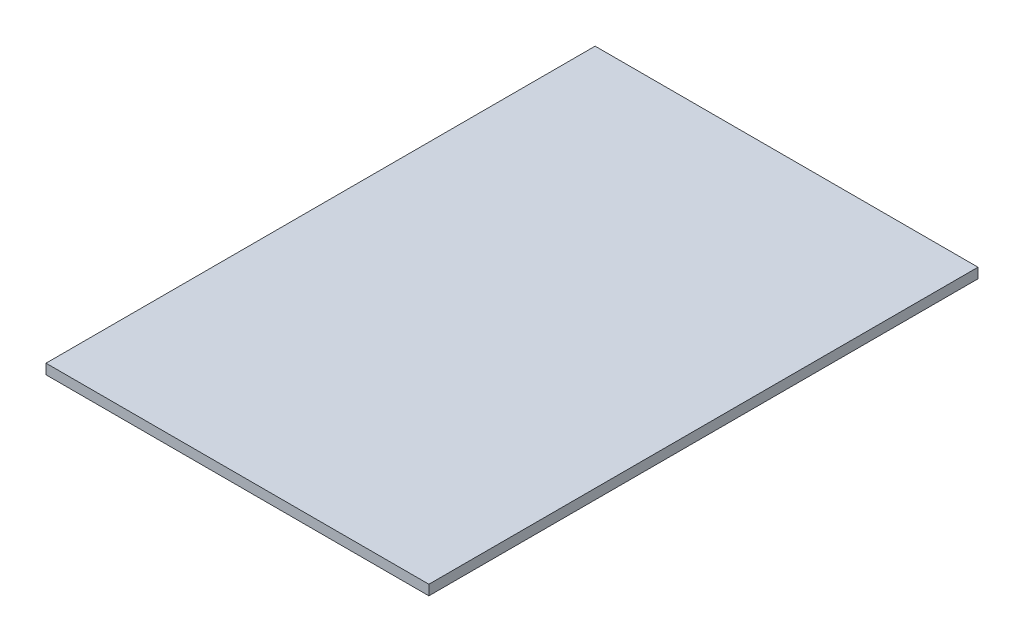
SolidWorks part; units mm, degrees
ref_plane "Front Plane" through (0, 0, 0) normal (0, 0, 1) x (1, 0, 0)
ref_plane "Top Plane" through (0, 0, 0) normal (0, 1, 0) x (1, 0, 0)
ref_plane "Right Plane" through (0, 0, 0) normal (1, 0, 0) x (0, 0, -1)
sketch "Sketch1" plane through (0, 0, 0) normal (0, 1, 0) x (1, 0, 0)
  line L0 (-74, 105) -> (-74, 109)
  line L1 (-74, 105) -> (74, 105) construction
  line L2 (-74, 105) -> (-74, -105)
  line L3 (-74, -105) -> (74, -105) construction
  line L4 (74, 105) -> (74, -105) construction
  line L5 (-74, 105) -> (74, -105) construction
  line L6 (-74, -105) -> (74, 105) construction
  line L7 (-74, 109) -> (78, 109)
  line L8 (78, 109) -> (78, -109)
  line L9 (78, -109) -> (-74, -109)
  line L10 (-74, -109) -> (-74, -105)
  line L11 (74, -105) -> (78, -105) construction
  point P0 (0, 0)
  dimension "D1" = 148
  dimension "D2" = 210
  dimension "D3" = 4
extrude "Boss-Extrude1" add sketch "Sketch1" along normal blind 4
sketch "Sketch2" plane through (0, 4, 0) normal (0, 1, 0) x (1, 0, 0)
  line L1 (72.0066, 102.0794) -> (78, 105.5397)
  line L2 (78, 105.5397) -> (78, 112.4603)
  line L3 (78, 112.4603) -> (72.0066, 115.9206)
  line L4 (72.0066, 115.9206) -> (66.0131, 112.4603)
  line L5 (66.0131, 112.4603) -> (66.0131, 105.5397)
  line L6 (66.0131, 105.5397) -> (72.0066, 102.0794)
  line L12 (72.0066, 109) -> (75.0033, 114.1905) construction
  line L19 (72.0066, 109) -> (78, 109) construction
  line L20 (78, 109) -> (-74, 109) construction
  line L21 (78, -109) -> (78, 109) construction
  line L22 (72.0066, 102.0794) -> (72.0066, 95.1587)
  line L23 (54.0262, 105.5397) -> (60.0197, 102.0794)
  line L24 (54.0262, 112.4603) -> (54.0262, 105.5397)
  line L25 (60.0197, 115.9206) -> (54.0262, 112.4603)
  line L26 (66.0131, 112.4603) -> (60.0197, 115.9206)
  line L27 (60.0197, 102.0794) -> (66.0131, 105.5397)
  line L28 (60.0197, 102.0794) -> (60.0197, 95.1587)
  line L29 (54.0262, 84.7778) -> (60.0197, 81.3175)
  line L30 (54.0262, 91.6984) -> (54.0262, 84.7778)
  line L31 (60.0197, 95.1587) -> (54.0262, 91.6984)
  line L32 (66.0131, 91.6984) -> (60.0197, 95.1587)
  line L33 (60.0197, 81.3175) -> (66.0131, 84.7778)
  line L34 (60.0197, 81.3175) -> (60.0197, 74.3968)
  line L35 (66.0131, 84.7778) -> (72.0066, 81.3175)
  line L36 (66.0131, 91.6984) -> (66.0131, 84.7778)
  line L37 (72.0066, 95.1587) -> (66.0131, 91.6984)
  line L38 (78, 91.6984) -> (72.0066, 95.1587)
  line L39 (72.0066, 81.3175) -> (78, 84.7778)
  line L40 (72.0066, 81.3175) -> (72.0066, 74.3968)
  line L41 (42.0393, 105.5397) -> (48.0328, 102.0794)
  line L42 (42.0393, 112.4603) -> (42.0393, 105.5397)
  line L43 (48.0328, 115.9206) -> (42.0393, 112.4603)
  line L44 (54.0262, 112.4603) -> (48.0328, 115.9206)
  line L45 (48.0328, 102.0794) -> (54.0262, 105.5397)
  line L46 (48.0328, 102.0794) -> (48.0328, 95.1587)
  line L47 (30.0524, 105.5397) -> (36.0459, 102.0794)
  line L48 (30.0524, 112.4603) -> (30.0524, 105.5397)
  line L49 (36.0459, 115.9206) -> (30.0524, 112.4603)
  line L50 (42.0393, 112.4603) -> (36.0459, 115.9206)
  line L51 (36.0459, 102.0794) -> (42.0393, 105.5397)
  line L52 (36.0459, 102.0794) -> (36.0459, 95.1587)
  line L53 (18.0655, 105.5397) -> (24.059, 102.0794)
  line L54 (18.0655, 112.4603) -> (18.0655, 105.5397)
  line L55 (24.059, 115.9206) -> (18.0655, 112.4603)
  line L56 (30.0524, 112.4603) -> (24.059, 115.9206)
  line L57 (24.059, 102.0794) -> (30.0524, 105.5397)
  line L58 (24.059, 102.0794) -> (24.059, 95.1587)
  line L59 (42.0393, 84.7778) -> (48.0328, 81.3175)
  line L60 (42.0393, 91.6984) -> (42.0393, 84.7778)
  line L61 (48.0328, 95.1587) -> (42.0393, 91.6984)
  line L62 (54.0262, 91.6984) -> (48.0328, 95.1587)
  line L63 (48.0328, 81.3175) -> (54.0262, 84.7778)
  line L64 (48.0328, 81.3175) -> (48.0328, 74.3968)
  line L65 (30.0524, 84.7778) -> (36.0459, 81.3175)
  line L66 (30.0524, 91.6984) -> (30.0524, 84.7778)
  line L67 (36.0459, 95.1587) -> (30.0524, 91.6984)
  line L68 (42.0393, 91.6984) -> (36.0459, 95.1587)
  line L69 (36.0459, 81.3175) -> (42.0393, 84.7778)
  line L70 (36.0459, 81.3175) -> (36.0459, 74.3968)
  line L71 (18.0655, 84.7778) -> (24.059, 81.3175)
  line L72 (18.0655, 91.6984) -> (18.0655, 84.7778)
  line L73 (24.059, 95.1587) -> (18.0655, 91.6984)
  line L74 (30.0524, 91.6984) -> (24.059, 95.1587)
  line L75 (24.059, 81.3175) -> (30.0524, 84.7778)
  line L76 (24.059, 81.3175) -> (24.059, 74.3968)
  line L77 (6.0787, 105.5397) -> (12.0721, 102.0794)
  line L78 (6.0787, 112.4603) -> (6.0787, 105.5397)
  line L79 (12.0721, 115.9206) -> (6.0787, 112.4603)
  line L80 (18.0655, 112.4603) -> (12.0721, 115.9206)
  line L81 (12.0721, 102.0794) -> (18.0655, 105.5397)
  line L82 (12.0721, 102.0794) -> (12.0721, 95.1587)
  line L83 (-5.9082, 105.5397) -> (0.0852, 102.0794)
  line L84 (-5.9082, 112.4603) -> (-5.9082, 105.5397)
  line L85 (0.0852, 115.9206) -> (-5.9082, 112.4603)
  line L86 (6.0787, 112.4603) -> (0.0852, 115.9206)
  line L87 (0.0852, 102.0794) -> (6.0787, 105.5397)
  line L88 (0.0852, 102.0794) -> (0.0852, 95.1587)
  line L89 (-17.8951, 105.5397) -> (-11.9017, 102.0794)
  line L90 (-17.8951, 112.4603) -> (-17.8951, 105.5397)
  line L91 (-11.9017, 115.9206) -> (-17.8951, 112.4603)
  line L92 (-5.9082, 112.4603) -> (-11.9017, 115.9206)
  line L93 (-11.9017, 102.0794) -> (-5.9082, 105.5397)
  line L94 (-11.9017, 102.0794) -> (-11.9017, 95.1587)
  line L95 (-29.882, 105.5397) -> (-23.8886, 102.0794)
  line L96 (-29.882, 112.4603) -> (-29.882, 105.5397)
  line L97 (-23.8886, 115.9206) -> (-29.882, 112.4603)
  line L98 (-17.8951, 112.4603) -> (-23.8886, 115.9206)
  line L99 (-23.8886, 102.0794) -> (-17.8951, 105.5397)
  line L100 (-23.8886, 102.0794) -> (-23.8886, 95.1587)
  line L101 (-41.8689, 105.5397) -> (-35.8755, 102.0794)
  line L102 (-41.8689, 112.4603) -> (-41.8689, 105.5397)
  line L103 (-35.8755, 115.9206) -> (-41.8689, 112.4603)
  line L104 (-29.882, 112.4603) -> (-35.8755, 115.9206)
  line L105 (-35.8755, 102.0794) -> (-29.882, 105.5397)
  line L106 (-35.8755, 102.0794) -> (-35.8755, 95.1587)
  line L107 (-53.8558, 105.5397) -> (-47.8624, 102.0794)
  line L108 (-53.8558, 112.4603) -> (-53.8558, 105.5397)
  line L109 (-47.8624, 115.9206) -> (-53.8558, 112.4603)
  line L110 (-41.8689, 112.4603) -> (-47.8624, 115.9206)
  line L111 (-47.8624, 102.0794) -> (-41.8689, 105.5397)
  line L112 (-47.8624, 102.0794) -> (-47.8624, 95.1587)
  line L113 (60.0197, -112.4603) -> (72.0066, -105.5397)
  line L114 (-74, -109) -> (78, -109) construction
  line L119 (6.0787, 84.7778) -> (12.0721, 81.3175)
  line L120 (6.0787, 91.6984) -> (6.0787, 84.7778)
  line L121 (12.0721, 95.1587) -> (6.0787, 91.6984)
  line L122 (18.0655, 91.6984) -> (12.0721, 95.1587)
  line L123 (12.0721, 81.3175) -> (18.0655, 84.7778)
  line L124 (12.0721, 81.3175) -> (12.0721, 74.3968)
  line L125 (-5.9082, 84.7778) -> (0.0852, 81.3175)
  line L126 (-5.9082, 91.6984) -> (-5.9082, 84.7778)
  line L127 (0.0852, 95.1587) -> (-5.9082, 91.6984)
  line L128 (6.0787, 91.6984) -> (0.0852, 95.1587)
  line L129 (0.0852, 81.3175) -> (6.0787, 84.7778)
  line L130 (0.0852, 81.3175) -> (0.0852, 74.3968)
  line L131 (-17.8951, 84.7778) -> (-11.9017, 81.3175)
  line L132 (-17.8951, 91.6984) -> (-17.8951, 84.7778)
  line L133 (-11.9017, 95.1587) -> (-17.8951, 91.6984)
  line L134 (-5.9082, 91.6984) -> (-11.9017, 95.1587)
  line L135 (-11.9017, 81.3175) -> (-5.9082, 84.7778)
  line L136 (-11.9017, 81.3175) -> (-11.9017, 74.3968)
  line L137 (-29.882, 84.7778) -> (-23.8886, 81.3175)
  line L138 (-29.882, 91.6984) -> (-29.882, 84.7778)
  line L139 (-23.8886, 95.1587) -> (-29.882, 91.6984)
  line L140 (-17.8951, 91.6984) -> (-23.8886, 95.1587)
  line L141 (-23.8886, 81.3175) -> (-17.8951, 84.7778)
  line L142 (-23.8886, 81.3175) -> (-23.8886, 74.3968)
  line L143 (-41.8689, 84.7778) -> (-35.8755, 81.3175)
  line L144 (-41.8689, 91.6984) -> (-41.8689, 84.7778)
  line L145 (-35.8755, 95.1587) -> (-41.8689, 91.6984)
  line L146 (-29.882, 91.6984) -> (-35.8755, 95.1587)
  line L147 (-35.8755, 81.3175) -> (-29.882, 84.7778)
  line L148 (-35.8755, 81.3175) -> (-35.8755, 74.3968)
  line L149 (-53.8558, 84.7778) -> (-47.8624, 81.3175)
  line L150 (-53.8558, 91.6984) -> (-53.8558, 84.7778)
  line L151 (-47.8624, 95.1587) -> (-53.8558, 91.6984)
  line L152 (-41.8689, 91.6984) -> (-47.8624, 95.1587)
  line L153 (-47.8624, 81.3175) -> (-41.8689, 84.7778)
  line L154 (-47.8624, 81.3175) -> (-47.8624, 74.3968)
  line L161 (66.0131, 64.0159) -> (72.0066, 60.5556)
  line L162 (66.0131, 70.9365) -> (66.0131, 64.0159)
  line L163 (72.0066, 74.3968) -> (66.0131, 70.9365)
  line L164 (78, 70.9365) -> (72.0066, 74.3968)
  line L165 (72.0066, 60.5556) -> (78, 64.0159)
  line L166 (72.0066, 60.5556) -> (72.0066, 53.6349)
  line L167 (54.0262, 64.0159) -> (60.0197, 60.5556)
  line L168 (54.0262, 70.9365) -> (54.0262, 64.0159)
  line L169 (60.0197, 74.3968) -> (54.0262, 70.9365)
  line L170 (66.0131, 70.9365) -> (60.0197, 74.3968)
  line L171 (60.0197, 60.5556) -> (66.0131, 64.0159)
  line L172 (60.0197, 60.5556) -> (60.0197, 53.6349)
  line L173 (42.0393, 64.0159) -> (48.0328, 60.5556)
  line L174 (42.0393, 70.9365) -> (42.0393, 64.0159)
  line L175 (48.0328, 74.3968) -> (42.0393, 70.9365)
  line L176 (54.0262, 70.9365) -> (48.0328, 74.3968)
  line L177 (48.0328, 60.5556) -> (54.0262, 64.0159)
  line L178 (48.0328, 60.5556) -> (48.0328, 53.6349)
  line L179 (30.0524, 64.0159) -> (36.0459, 60.5556)
  line L180 (30.0524, 70.9365) -> (30.0524, 64.0159)
  line L181 (36.0459, 74.3968) -> (30.0524, 70.9365)
  line L182 (42.0393, 70.9365) -> (36.0459, 74.3968)
  line L183 (36.0459, 60.5556) -> (42.0393, 64.0159)
  line L184 (36.0459, 60.5556) -> (36.0459, 53.6349)
  line L185 (18.0655, 64.0159) -> (24.059, 60.5556)
  line L186 (18.0655, 70.9365) -> (18.0655, 64.0159)
  line L187 (24.059, 74.3968) -> (18.0655, 70.9365)
  line L188 (30.0524, 70.9365) -> (24.059, 74.3968)
  line L189 (24.059, 60.5556) -> (30.0524, 64.0159)
  line L190 (24.059, 60.5556) -> (24.059, 53.6349)
  line L191 (6.0787, 64.0159) -> (12.0721, 60.5556)
  line L192 (6.0787, 70.9365) -> (6.0787, 64.0159)
  line L193 (12.0721, 74.3968) -> (6.0787, 70.9365)
  line L194 (18.0655, 70.9365) -> (12.0721, 74.3968)
  line L195 (12.0721, 60.5556) -> (18.0655, 64.0159)
  line L196 (12.0721, 60.5556) -> (12.0721, 53.6349)
  line L197 (-5.9082, 64.0159) -> (0.0852, 60.5556)
  line L198 (-5.9082, 70.9365) -> (-5.9082, 64.0159)
  line L199 (0.0852, 74.3968) -> (-5.9082, 70.9365)
  line L200 (6.0787, 70.9365) -> (0.0852, 74.3968)
  line L201 (0.0852, 60.5556) -> (6.0787, 64.0159)
  line L202 (0.0852, 60.5556) -> (0.0852, 53.6349)
  line L203 (-17.8951, 64.0159) -> (-11.9017, 60.5556)
  line L204 (-17.8951, 70.9365) -> (-17.8951, 64.0159)
  line L205 (-11.9017, 74.3968) -> (-17.8951, 70.9365)
  line L206 (-5.9082, 70.9365) -> (-11.9017, 74.3968)
  line L207 (-11.9017, 60.5556) -> (-5.9082, 64.0159)
  line L208 (-11.9017, 60.5556) -> (-11.9017, 53.6349)
  line L209 (-29.882, 64.0159) -> (-23.8886, 60.5556)
  line L210 (-29.882, 70.9365) -> (-29.882, 64.0159)
  line L211 (-23.8886, 74.3968) -> (-29.882, 70.9365)
  line L212 (-17.8951, 70.9365) -> (-23.8886, 74.3968)
  line L213 (-23.8886, 60.5556) -> (-17.8951, 64.0159)
  line L214 (-23.8886, 60.5556) -> (-23.8886, 53.6349)
  line L215 (-41.8689, 64.0159) -> (-35.8755, 60.5556)
  line L216 (-41.8689, 70.9365) -> (-41.8689, 64.0159)
  line L217 (-35.8755, 74.3968) -> (-41.8689, 70.9365)
  line L218 (-29.882, 70.9365) -> (-35.8755, 74.3968)
  line L219 (-35.8755, 60.5556) -> (-29.882, 64.0159)
  line L220 (-35.8755, 60.5556) -> (-35.8755, 53.6349)
  line L221 (-53.8558, 64.0159) -> (-47.8624, 60.5556)
  line L222 (-53.8558, 70.9365) -> (-53.8558, 64.0159)
  line L223 (-47.8624, 74.3968) -> (-53.8558, 70.9365)
  line L224 (-41.8689, 70.9365) -> (-47.8624, 74.3968)
  line L225 (-47.8624, 60.5556) -> (-41.8689, 64.0159)
  line L226 (-47.8624, 60.5556) -> (-47.8624, 53.6349)
  line L233 (66.0131, 43.254) -> (72.0066, 39.7937)
  line L234 (66.0131, 50.1746) -> (66.0131, 43.254)
  line L235 (72.0066, 53.6349) -> (66.0131, 50.1746)
  line L236 (78, 50.1746) -> (72.0066, 53.6349)
  line L237 (72.0066, 39.7937) -> (78, 43.254)
  line L238 (72.0066, 39.7937) -> (72.0066, 32.873)
  line L239 (54.0262, 43.254) -> (60.0197, 39.7937)
  line L240 (54.0262, 50.1746) -> (54.0262, 43.254)
  line L241 (60.0197, 53.6349) -> (54.0262, 50.1746)
  line L242 (66.0131, 50.1746) -> (60.0197, 53.6349)
  line L243 (60.0197, 39.7937) -> (66.0131, 43.254)
  line L244 (60.0197, 39.7937) -> (60.0197, 32.873)
  line L245 (42.0393, 43.254) -> (48.0328, 39.7937)
  line L246 (42.0393, 50.1746) -> (42.0393, 43.254)
  line L247 (48.0328, 53.6349) -> (42.0393, 50.1746)
  line L248 (54.0262, 50.1746) -> (48.0328, 53.6349)
  line L249 (48.0328, 39.7937) -> (54.0262, 43.254)
  line L250 (48.0328, 39.7937) -> (48.0328, 32.873)
  line L251 (30.0524, 43.254) -> (36.0459, 39.7937)
  line L252 (30.0524, 50.1746) -> (30.0524, 43.254)
  line L253 (36.0459, 53.6349) -> (30.0524, 50.1746)
  line L254 (42.0393, 50.1746) -> (36.0459, 53.6349)
  line L255 (36.0459, 39.7937) -> (42.0393, 43.254)
  line L256 (36.0459, 39.7937) -> (36.0459, 32.873)
  line L257 (18.0655, 43.254) -> (24.059, 39.7937)
  line L258 (18.0655, 50.1746) -> (18.0655, 43.254)
  line L259 (24.059, 53.6349) -> (18.0655, 50.1746)
  line L260 (30.0524, 50.1746) -> (24.059, 53.6349)
  line L261 (24.059, 39.7937) -> (30.0524, 43.254)
  line L262 (24.059, 39.7937) -> (24.059, 32.873)
  line L263 (6.0787, 43.254) -> (12.0721, 39.7937)
  line L264 (6.0787, 50.1746) -> (6.0787, 43.254)
  line L265 (12.0721, 53.6349) -> (6.0787, 50.1746)
  line L266 (18.0655, 50.1746) -> (12.0721, 53.6349)
  line L267 (12.0721, 39.7937) -> (18.0655, 43.254)
  line L268 (12.0721, 39.7937) -> (12.0721, 32.873)
  line L269 (-5.9082, 43.254) -> (0.0852, 39.7937)
  line L270 (-5.9082, 50.1746) -> (-5.9082, 43.254)
  line L271 (0.0852, 53.6349) -> (-5.9082, 50.1746)
  line L272 (6.0787, 50.1746) -> (0.0852, 53.6349)
  line L273 (0.0852, 39.7937) -> (6.0787, 43.254)
  line L274 (0.0852, 39.7937) -> (0.0852, 32.873)
  line L275 (-17.8951, 43.254) -> (-11.9017, 39.7937)
  line L276 (-17.8951, 50.1746) -> (-17.8951, 43.254)
  line L277 (-11.9017, 53.6349) -> (-17.8951, 50.1746)
  line L278 (-5.9082, 50.1746) -> (-11.9017, 53.6349)
  line L279 (-11.9017, 39.7937) -> (-5.9082, 43.254)
  line L280 (-11.9017, 39.7937) -> (-11.9017, 32.873)
  line L281 (-29.882, 43.254) -> (-23.8886, 39.7937)
  line L282 (-29.882, 50.1746) -> (-29.882, 43.254)
  line L283 (-23.8886, 53.6349) -> (-29.882, 50.1746)
  line L284 (-17.8951, 50.1746) -> (-23.8886, 53.6349)
  line L285 (-23.8886, 39.7937) -> (-17.8951, 43.254)
  line L286 (-23.8886, 39.7937) -> (-23.8886, 32.873)
  line L287 (-41.8689, 43.254) -> (-35.8755, 39.7937)
  line L288 (-41.8689, 50.1746) -> (-41.8689, 43.254)
  line L289 (-35.8755, 53.6349) -> (-41.8689, 50.1746)
  line L290 (-29.882, 50.1746) -> (-35.8755, 53.6349)
  line L291 (-35.8755, 39.7937) -> (-29.882, 43.254)
  line L292 (-35.8755, 39.7937) -> (-35.8755, 32.873)
  line L293 (-53.8558, 43.254) -> (-47.8624, 39.7937)
  line L294 (-53.8558, 50.1746) -> (-53.8558, 43.254)
  line L295 (-47.8624, 53.6349) -> (-53.8558, 50.1746)
  line L296 (-41.8689, 50.1746) -> (-47.8624, 53.6349)
  line L297 (-47.8624, 39.7937) -> (-41.8689, 43.254)
  line L298 (-47.8624, 39.7937) -> (-47.8624, 32.873)
  line L305 (66.0131, 22.4921) -> (72.0066, 19.0317)
  line L306 (66.0131, 29.4127) -> (66.0131, 22.4921)
  line L307 (72.0066, 32.873) -> (66.0131, 29.4127)
  line L308 (78, 29.4127) -> (72.0066, 32.873)
  line L309 (72.0066, 19.0317) -> (78, 22.4921)
  line L310 (72.0066, 19.0317) -> (72.0066, 12.1111)
  line L311 (54.0262, 22.4921) -> (60.0197, 19.0317)
  line L312 (54.0262, 29.4127) -> (54.0262, 22.4921)
  line L313 (60.0197, 32.873) -> (54.0262, 29.4127)
  line L314 (66.0131, 29.4127) -> (60.0197, 32.873)
  line L315 (60.0197, 19.0317) -> (66.0131, 22.4921)
  line L316 (60.0197, 19.0317) -> (60.0197, 12.1111)
  line L317 (42.0393, 22.4921) -> (48.0328, 19.0317)
  line L318 (42.0393, 29.4127) -> (42.0393, 22.4921)
  line L319 (48.0328, 32.873) -> (42.0393, 29.4127)
  line L320 (54.0262, 29.4127) -> (48.0328, 32.873)
  line L321 (48.0328, 19.0317) -> (54.0262, 22.4921)
  line L322 (48.0328, 19.0317) -> (48.0328, 12.1111)
  line L323 (30.0524, 22.4921) -> (36.0459, 19.0317)
  line L324 (30.0524, 29.4127) -> (30.0524, 22.4921)
  line L325 (36.0459, 32.873) -> (30.0524, 29.4127)
  line L326 (42.0393, 29.4127) -> (36.0459, 32.873)
  line L327 (36.0459, 19.0317) -> (42.0393, 22.4921)
  line L328 (36.0459, 19.0317) -> (36.0459, 12.1111)
  line L329 (18.0655, 22.4921) -> (24.059, 19.0317)
  line L330 (18.0655, 29.4127) -> (18.0655, 22.4921)
  line L331 (24.059, 32.873) -> (18.0655, 29.4127)
  line L332 (30.0524, 29.4127) -> (24.059, 32.873)
  line L333 (24.059, 19.0317) -> (30.0524, 22.4921)
  line L334 (24.059, 19.0317) -> (24.059, 12.1111)
  line L335 (6.0787, 22.4921) -> (12.0721, 19.0317)
  line L336 (6.0787, 29.4127) -> (6.0787, 22.4921)
  line L337 (12.0721, 32.873) -> (6.0787, 29.4127)
  line L338 (18.0655, 29.4127) -> (12.0721, 32.873)
  line L339 (12.0721, 19.0317) -> (18.0655, 22.4921)
  line L340 (12.0721, 19.0317) -> (12.0721, 12.1111)
  line L341 (-5.9082, 22.4921) -> (0.0852, 19.0317)
  line L342 (-5.9082, 29.4127) -> (-5.9082, 22.4921)
  line L343 (0.0852, 32.873) -> (-5.9082, 29.4127)
  line L344 (6.0787, 29.4127) -> (0.0852, 32.873)
  line L345 (0.0852, 19.0317) -> (6.0787, 22.4921)
  line L346 (0.0852, 19.0317) -> (0.0852, 12.1111)
  line L347 (-17.8951, 22.4921) -> (-11.9017, 19.0317)
  line L348 (-17.8951, 29.4127) -> (-17.8951, 22.4921)
  line L349 (-11.9017, 32.873) -> (-17.8951, 29.4127)
  line L350 (-5.9082, 29.4127) -> (-11.9017, 32.873)
  line L351 (-11.9017, 19.0317) -> (-5.9082, 22.4921)
  line L352 (-11.9017, 19.0317) -> (-11.9017, 12.1111)
  line L353 (-29.882, 22.4921) -> (-23.8886, 19.0317)
  line L354 (-29.882, 29.4127) -> (-29.882, 22.4921)
  line L355 (-23.8886, 32.873) -> (-29.882, 29.4127)
  line L356 (-17.8951, 29.4127) -> (-23.8886, 32.873)
  line L357 (-23.8886, 19.0317) -> (-17.8951, 22.4921)
  line L358 (-23.8886, 19.0317) -> (-23.8886, 12.1111)
  line L359 (-41.8689, 22.4921) -> (-35.8755, 19.0317)
  line L360 (-41.8689, 29.4127) -> (-41.8689, 22.4921)
  line L361 (-35.8755, 32.873) -> (-41.8689, 29.4127)
  line L362 (-29.882, 29.4127) -> (-35.8755, 32.873)
  line L363 (-35.8755, 19.0317) -> (-29.882, 22.4921)
  line L364 (-35.8755, 19.0317) -> (-35.8755, 12.1111)
  line L365 (-53.8558, 22.4921) -> (-47.8624, 19.0317)
  line L366 (-53.8558, 29.4127) -> (-53.8558, 22.4921)
  line L367 (-47.8624, 32.873) -> (-53.8558, 29.4127)
  line L368 (-41.8689, 29.4127) -> (-47.8624, 32.873)
  line L369 (-47.8624, 19.0317) -> (-41.8689, 22.4921)
  line L370 (-47.8624, 19.0317) -> (-47.8624, 12.1111)
  line L377 (66.0131, 1.7302) -> (72.0066, -1.7302)
  line L378 (66.0131, 8.6508) -> (66.0131, 1.7302)
  line L379 (72.0066, 12.1111) -> (66.0131, 8.6508)
  line L380 (78, 8.6508) -> (72.0066, 12.1111)
  line L381 (72.0066, -1.7302) -> (78, 1.7302)
  line L382 (72.0066, -1.7302) -> (72.0066, -8.6508)
  line L383 (54.0262, 1.7302) -> (60.0197, -1.7302)
  line L384 (54.0262, 8.6508) -> (54.0262, 1.7302)
  line L385 (60.0197, 12.1111) -> (54.0262, 8.6508)
  line L386 (66.0131, 8.6508) -> (60.0197, 12.1111)
  line L387 (60.0197, -1.7302) -> (66.0131, 1.7302)
  line L388 (60.0197, -1.7302) -> (60.0197, -8.6508)
  line L389 (42.0393, 1.7302) -> (48.0328, -1.7302)
  line L390 (42.0393, 8.6508) -> (42.0393, 1.7302)
  line L391 (48.0328, 12.1111) -> (42.0393, 8.6508)
  line L392 (54.0262, 8.6508) -> (48.0328, 12.1111)
  line L393 (48.0328, -1.7302) -> (54.0262, 1.7302)
  line L394 (48.0328, -1.7302) -> (48.0328, -8.6508)
  line L395 (30.0524, 1.7302) -> (36.0459, -1.7302)
  line L396 (30.0524, 8.6508) -> (30.0524, 1.7302)
  line L397 (36.0459, 12.1111) -> (30.0524, 8.6508)
  line L398 (42.0393, 8.6508) -> (36.0459, 12.1111)
  line L399 (36.0459, -1.7302) -> (42.0393, 1.7302)
  line L400 (36.0459, -1.7302) -> (36.0459, -8.6508)
  line L401 (18.0655, 1.7302) -> (24.059, -1.7302)
  line L402 (18.0655, 8.6508) -> (18.0655, 1.7302)
  line L403 (24.059, 12.1111) -> (18.0655, 8.6508)
  line L404 (30.0524, 8.6508) -> (24.059, 12.1111)
  line L405 (24.059, -1.7302) -> (30.0524, 1.7302)
  line L406 (24.059, -1.7302) -> (24.059, -8.6508)
  line L407 (6.0787, 1.7302) -> (12.0721, -1.7302)
  line L408 (6.0787, 8.6508) -> (6.0787, 1.7302)
  line L409 (12.0721, 12.1111) -> (6.0787, 8.6508)
  line L410 (18.0655, 8.6508) -> (12.0721, 12.1111)
  line L411 (12.0721, -1.7302) -> (18.0655, 1.7302)
  line L412 (12.0721, -1.7302) -> (12.0721, -8.6508)
  line L413 (-5.9082, 1.7302) -> (0.0852, -1.7302)
  line L414 (-5.9082, 8.6508) -> (-5.9082, 1.7302)
  line L415 (0.0852, 12.1111) -> (-5.9082, 8.6508)
  line L416 (6.0787, 8.6508) -> (0.0852, 12.1111)
  line L417 (0.0852, -1.7302) -> (6.0787, 1.7302)
  line L418 (0.0852, -1.7302) -> (0.0852, -8.6508)
  line L419 (-17.8951, 1.7302) -> (-11.9017, -1.7302)
  line L420 (-17.8951, 8.6508) -> (-17.8951, 1.7302)
  line L421 (-11.9017, 12.1111) -> (-17.8951, 8.6508)
  line L422 (-5.9082, 8.6508) -> (-11.9017, 12.1111)
  line L423 (-11.9017, -1.7302) -> (-5.9082, 1.7302)
  line L424 (-11.9017, -1.7302) -> (-11.9017, -8.6508)
  line L425 (-29.882, 1.7302) -> (-23.8886, -1.7302)
  line L426 (-29.882, 8.6508) -> (-29.882, 1.7302)
  line L427 (-23.8886, 12.1111) -> (-29.882, 8.6508)
  line L428 (-17.8951, 8.6508) -> (-23.8886, 12.1111)
  line L429 (-23.8886, -1.7302) -> (-17.8951, 1.7302)
  line L430 (-23.8886, -1.7302) -> (-23.8886, -8.6508)
  line L431 (-41.8689, 1.7302) -> (-35.8755, -1.7302)
  line L432 (-41.8689, 8.6508) -> (-41.8689, 1.7302)
  line L433 (-35.8755, 12.1111) -> (-41.8689, 8.6508)
  line L434 (-29.882, 8.6508) -> (-35.8755, 12.1111)
  line L435 (-35.8755, -1.7302) -> (-29.882, 1.7302)
  line L436 (-35.8755, -1.7302) -> (-35.8755, -8.6508)
  line L437 (-53.8558, 1.7302) -> (-47.8624, -1.7302)
  line L438 (-53.8558, 8.6508) -> (-53.8558, 1.7302)
  line L439 (-47.8624, 12.1111) -> (-53.8558, 8.6508)
  line L440 (-41.8689, 8.6508) -> (-47.8624, 12.1111)
  line L441 (-47.8624, -1.7302) -> (-41.8689, 1.7302)
  line L442 (-47.8624, -1.7302) -> (-47.8624, -8.6508)
  line L449 (66.0131, -19.0317) -> (72.0066, -22.4921)
  line L450 (66.0131, -12.1111) -> (66.0131, -19.0317)
  line L451 (72.0066, -8.6508) -> (66.0131, -12.1111)
  line L452 (78, -12.1111) -> (72.0066, -8.6508)
  line L453 (72.0066, -22.4921) -> (78, -19.0317)
  line L454 (72.0066, -22.4921) -> (72.0066, -29.4127)
  line L455 (54.0262, -19.0317) -> (60.0197, -22.4921)
  line L456 (54.0262, -12.1111) -> (54.0262, -19.0317)
  line L457 (60.0197, -8.6508) -> (54.0262, -12.1111)
  line L458 (66.0131, -12.1111) -> (60.0197, -8.6508)
  line L459 (60.0197, -22.4921) -> (66.0131, -19.0317)
  line L460 (60.0197, -22.4921) -> (60.0197, -29.4127)
  line L461 (42.0393, -19.0317) -> (48.0328, -22.4921)
  line L462 (42.0393, -12.1111) -> (42.0393, -19.0317)
  line L463 (48.0328, -8.6508) -> (42.0393, -12.1111)
  line L464 (54.0262, -12.1111) -> (48.0328, -8.6508)
  line L465 (48.0328, -22.4921) -> (54.0262, -19.0317)
  line L466 (48.0328, -22.4921) -> (48.0328, -29.4127)
  line L467 (30.0524, -19.0317) -> (36.0459, -22.4921)
  line L468 (30.0524, -12.1111) -> (30.0524, -19.0317)
  line L469 (36.0459, -8.6508) -> (30.0524, -12.1111)
  line L470 (42.0393, -12.1111) -> (36.0459, -8.6508)
  line L471 (36.0459, -22.4921) -> (42.0393, -19.0317)
  line L472 (36.0459, -22.4921) -> (36.0459, -29.4127)
  line L473 (18.0655, -19.0317) -> (24.059, -22.4921)
  line L474 (18.0655, -12.1111) -> (18.0655, -19.0317)
  line L475 (24.059, -8.6508) -> (18.0655, -12.1111)
  line L476 (30.0524, -12.1111) -> (24.059, -8.6508)
  line L477 (24.059, -22.4921) -> (30.0524, -19.0317)
  line L478 (24.059, -22.4921) -> (24.059, -29.4127)
  line L479 (6.0787, -19.0317) -> (12.0721, -22.4921)
  line L480 (6.0787, -12.1111) -> (6.0787, -19.0317)
  line L481 (12.0721, -8.6508) -> (6.0787, -12.1111)
  line L482 (18.0655, -12.1111) -> (12.0721, -8.6508)
  line L483 (12.0721, -22.4921) -> (18.0655, -19.0317)
  line L484 (12.0721, -22.4921) -> (12.0721, -29.4127)
  line L485 (-5.9082, -19.0317) -> (0.0852, -22.4921)
  line L486 (-5.9082, -12.1111) -> (-5.9082, -19.0317)
  line L487 (0.0852, -8.6508) -> (-5.9082, -12.1111)
  line L488 (6.0787, -12.1111) -> (0.0852, -8.6508)
  line L489 (0.0852, -22.4921) -> (6.0787, -19.0317)
  line L490 (0.0852, -22.4921) -> (0.0852, -29.4127)
  line L491 (-17.8951, -19.0317) -> (-11.9017, -22.4921)
  line L492 (-17.8951, -12.1111) -> (-17.8951, -19.0317)
  line L493 (-11.9017, -8.6508) -> (-17.8951, -12.1111)
  line L494 (-5.9082, -12.1111) -> (-11.9017, -8.6508)
  line L495 (-11.9017, -22.4921) -> (-5.9082, -19.0317)
  line L496 (-11.9017, -22.4921) -> (-11.9017, -29.4127)
  line L497 (-29.882, -19.0317) -> (-23.8886, -22.4921)
  line L498 (-29.882, -12.1111) -> (-29.882, -19.0317)
  line L499 (-23.8886, -8.6508) -> (-29.882, -12.1111)
  line L500 (-17.8951, -12.1111) -> (-23.8886, -8.6508)
  line L501 (-23.8886, -22.4921) -> (-17.8951, -19.0317)
  line L502 (-23.8886, -22.4921) -> (-23.8886, -29.4127)
  line L503 (-41.8689, -19.0317) -> (-35.8755, -22.4921)
  line L504 (-41.8689, -12.1111) -> (-41.8689, -19.0317)
  line L505 (-35.8755, -8.6508) -> (-41.8689, -12.1111)
  line L506 (-29.882, -12.1111) -> (-35.8755, -8.6508)
  line L507 (-35.8755, -22.4921) -> (-29.882, -19.0317)
  line L508 (-35.8755, -22.4921) -> (-35.8755, -29.4127)
  line L509 (-53.8558, -19.0317) -> (-47.8624, -22.4921)
  line L510 (-53.8558, -12.1111) -> (-53.8558, -19.0317)
  line L511 (-47.8624, -8.6508) -> (-53.8558, -12.1111)
  line L512 (-41.8689, -12.1111) -> (-47.8624, -8.6508)
  line L513 (-47.8624, -22.4921) -> (-41.8689, -19.0317)
  line L514 (-47.8624, -22.4921) -> (-47.8624, -29.4127)
  line L521 (66.0131, -39.7937) -> (72.0066, -43.254)
  line L522 (66.0131, -32.873) -> (66.0131, -39.7937)
  line L523 (72.0066, -29.4127) -> (66.0131, -32.873)
  line L524 (78, -32.873) -> (72.0066, -29.4127)
  line L525 (72.0066, -43.254) -> (78, -39.7937)
  line L526 (72.0066, -43.254) -> (72.0066, -50.1746)
  line L527 (54.0262, -39.7937) -> (60.0197, -43.254)
  line L528 (54.0262, -32.873) -> (54.0262, -39.7937)
  line L529 (60.0197, -29.4127) -> (54.0262, -32.873)
  line L530 (66.0131, -32.873) -> (60.0197, -29.4127)
  line L531 (60.0197, -43.254) -> (66.0131, -39.7937)
  line L532 (60.0197, -43.254) -> (60.0197, -50.1746)
  line L533 (42.0393, -39.7937) -> (48.0328, -43.254)
  line L534 (42.0393, -32.873) -> (42.0393, -39.7937)
  line L535 (48.0328, -29.4127) -> (42.0393, -32.873)
  line L536 (54.0262, -32.873) -> (48.0328, -29.4127)
  line L537 (48.0328, -43.254) -> (54.0262, -39.7937)
  line L538 (48.0328, -43.254) -> (48.0328, -50.1746)
  line L539 (30.0524, -39.7937) -> (36.0459, -43.254)
  line L540 (30.0524, -32.873) -> (30.0524, -39.7937)
  line L541 (36.0459, -29.4127) -> (30.0524, -32.873)
  line L542 (42.0393, -32.873) -> (36.0459, -29.4127)
  line L543 (36.0459, -43.254) -> (42.0393, -39.7937)
  line L544 (36.0459, -43.254) -> (36.0459, -50.1746)
  line L545 (18.0655, -39.7937) -> (24.059, -43.254)
  line L546 (18.0655, -32.873) -> (18.0655, -39.7937)
  line L547 (24.059, -29.4127) -> (18.0655, -32.873)
  line L548 (30.0524, -32.873) -> (24.059, -29.4127)
  line L549 (24.059, -43.254) -> (30.0524, -39.7937)
  line L550 (24.059, -43.254) -> (24.059, -50.1746)
  line L551 (6.0787, -39.7937) -> (12.0721, -43.254)
  line L552 (6.0787, -32.873) -> (6.0787, -39.7937)
  line L553 (12.0721, -29.4127) -> (6.0787, -32.873)
  line L554 (18.0655, -32.873) -> (12.0721, -29.4127)
  line L555 (12.0721, -43.254) -> (18.0655, -39.7937)
  line L556 (12.0721, -43.254) -> (12.0721, -50.1746)
  line L557 (-5.9082, -39.7937) -> (0.0852, -43.254)
  line L558 (-5.9082, -32.873) -> (-5.9082, -39.7937)
  line L559 (0.0852, -29.4127) -> (-5.9082, -32.873)
  line L560 (6.0787, -32.873) -> (0.0852, -29.4127)
  line L561 (0.0852, -43.254) -> (6.0787, -39.7937)
  line L562 (0.0852, -43.254) -> (0.0852, -50.1746)
  line L563 (-17.8951, -39.7937) -> (-11.9017, -43.254)
  line L564 (-17.8951, -32.873) -> (-17.8951, -39.7937)
  line L565 (-11.9017, -29.4127) -> (-17.8951, -32.873)
  line L566 (-5.9082, -32.873) -> (-11.9017, -29.4127)
  line L567 (-11.9017, -43.254) -> (-5.9082, -39.7937)
  line L568 (-11.9017, -43.254) -> (-11.9017, -50.1746)
  line L569 (-29.882, -39.7937) -> (-23.8886, -43.254)
  line L570 (-29.882, -32.873) -> (-29.882, -39.7937)
  line L571 (-23.8886, -29.4127) -> (-29.882, -32.873)
  line L572 (-17.8951, -32.873) -> (-23.8886, -29.4127)
  line L573 (-23.8886, -43.254) -> (-17.8951, -39.7937)
  line L574 (-23.8886, -43.254) -> (-23.8886, -50.1746)
  line L575 (-41.8689, -39.7937) -> (-35.8755, -43.254)
  line L576 (-41.8689, -32.873) -> (-41.8689, -39.7937)
  line L577 (-35.8755, -29.4127) -> (-41.8689, -32.873)
  line L578 (-29.882, -32.873) -> (-35.8755, -29.4127)
  line L579 (-35.8755, -43.254) -> (-29.882, -39.7937)
  line L580 (-35.8755, -43.254) -> (-35.8755, -50.1746)
  line L581 (-53.8558, -39.7937) -> (-47.8624, -43.254)
  line L582 (-53.8558, -32.873) -> (-53.8558, -39.7937)
  line L583 (-47.8624, -29.4127) -> (-53.8558, -32.873)
  line L584 (-41.8689, -32.873) -> (-47.8624, -29.4127)
  line L585 (-47.8624, -43.254) -> (-41.8689, -39.7937)
  line L586 (-47.8624, -43.254) -> (-47.8624, -50.1746)
  line L593 (66.0131, -60.5556) -> (72.0066, -64.0159)
  line L594 (66.0131, -53.6349) -> (66.0131, -60.5556)
  line L595 (72.0066, -50.1746) -> (66.0131, -53.6349)
  line L596 (78, -53.6349) -> (72.0066, -50.1746)
  line L597 (72.0066, -64.0159) -> (78, -60.5556)
  line L598 (72.0066, -64.0159) -> (72.0066, -70.9365)
  line L599 (54.0262, -60.5556) -> (60.0197, -64.0159)
  line L600 (54.0262, -53.6349) -> (54.0262, -60.5556)
  line L601 (60.0197, -50.1746) -> (54.0262, -53.6349)
  line L602 (66.0131, -53.6349) -> (60.0197, -50.1746)
  line L603 (60.0197, -64.0159) -> (66.0131, -60.5556)
  line L604 (60.0197, -64.0159) -> (60.0197, -70.9365)
  line L605 (42.0393, -60.5556) -> (48.0328, -64.0159)
  line L606 (42.0393, -53.6349) -> (42.0393, -60.5556)
  line L607 (48.0328, -50.1746) -> (42.0393, -53.6349)
  line L608 (54.0262, -53.6349) -> (48.0328, -50.1746)
  line L609 (48.0328, -64.0159) -> (54.0262, -60.5556)
  line L610 (48.0328, -64.0159) -> (48.0328, -70.9365)
  line L611 (30.0524, -60.5556) -> (36.0459, -64.0159)
  line L612 (30.0524, -53.6349) -> (30.0524, -60.5556)
  line L613 (36.0459, -50.1746) -> (30.0524, -53.6349)
  line L614 (42.0393, -53.6349) -> (36.0459, -50.1746)
  line L615 (36.0459, -64.0159) -> (42.0393, -60.5556)
  line L616 (36.0459, -64.0159) -> (36.0459, -70.9365)
  line L617 (18.0655, -60.5556) -> (24.059, -64.0159)
  line L618 (18.0655, -53.6349) -> (18.0655, -60.5556)
  line L619 (24.059, -50.1746) -> (18.0655, -53.6349)
  line L620 (30.0524, -53.6349) -> (24.059, -50.1746)
  line L621 (24.059, -64.0159) -> (30.0524, -60.5556)
  line L622 (24.059, -64.0159) -> (24.059, -70.9365)
  line L623 (6.0787, -60.5556) -> (12.0721, -64.0159)
  line L624 (6.0787, -53.6349) -> (6.0787, -60.5556)
  line L625 (12.0721, -50.1746) -> (6.0787, -53.6349)
  line L626 (18.0655, -53.6349) -> (12.0721, -50.1746)
  line L627 (12.0721, -64.0159) -> (18.0655, -60.5556)
  line L628 (12.0721, -64.0159) -> (12.0721, -70.9365)
  line L629 (-5.9082, -60.5556) -> (0.0852, -64.0159)
  line L630 (-5.9082, -53.6349) -> (-5.9082, -60.5556)
  line L631 (0.0852, -50.1746) -> (-5.9082, -53.6349)
  line L632 (6.0787, -53.6349) -> (0.0852, -50.1746)
  line L633 (0.0852, -64.0159) -> (6.0787, -60.5556)
  line L634 (0.0852, -64.0159) -> (0.0852, -70.9365)
  line L635 (-17.8951, -60.5556) -> (-11.9017, -64.0159)
  line L636 (-17.8951, -53.6349) -> (-17.8951, -60.5556)
  line L637 (-11.9017, -50.1746) -> (-17.8951, -53.6349)
  line L638 (-5.9082, -53.6349) -> (-11.9017, -50.1746)
  line L639 (-11.9017, -64.0159) -> (-5.9082, -60.5556)
  line L640 (-11.9017, -64.0159) -> (-11.9017, -70.9365)
  line L641 (-29.882, -60.5556) -> (-23.8886, -64.0159)
  line L642 (-29.882, -53.6349) -> (-29.882, -60.5556)
  line L643 (-23.8886, -50.1746) -> (-29.882, -53.6349)
  line L644 (-17.8951, -53.6349) -> (-23.8886, -50.1746)
  line L645 (-23.8886, -64.0159) -> (-17.8951, -60.5556)
  line L646 (-23.8886, -64.0159) -> (-23.8886, -70.9365)
  line L647 (-41.8689, -60.5556) -> (-35.8755, -64.0159)
  line L648 (-41.8689, -53.6349) -> (-41.8689, -60.5556)
  line L649 (-35.8755, -50.1746) -> (-41.8689, -53.6349)
  line L650 (-29.882, -53.6349) -> (-35.8755, -50.1746)
  line L651 (-35.8755, -64.0159) -> (-29.882, -60.5556)
  line L652 (-35.8755, -64.0159) -> (-35.8755, -70.9365)
  line L653 (-53.8558, -60.5556) -> (-47.8624, -64.0159)
  line L654 (-53.8558, -53.6349) -> (-53.8558, -60.5556)
  line L655 (-47.8624, -50.1746) -> (-53.8558, -53.6349)
  line L656 (-41.8689, -53.6349) -> (-47.8624, -50.1746)
  line L657 (-47.8624, -64.0159) -> (-41.8689, -60.5556)
  line L658 (-47.8624, -64.0159) -> (-47.8624, -70.9365)
  line L665 (66.0131, -81.3175) -> (72.0066, -84.7778)
  line L666 (66.0131, -74.3968) -> (66.0131, -81.3175)
  line L667 (72.0066, -70.9365) -> (66.0131, -74.3968)
  line L668 (78, -74.3968) -> (72.0066, -70.9365)
  line L669 (72.0066, -84.7778) -> (78, -81.3175)
  line L670 (72.0066, -84.7778) -> (72.0066, -91.6984)
  line L671 (54.0262, -81.3175) -> (60.0197, -84.7778)
  line L672 (54.0262, -74.3968) -> (54.0262, -81.3175)
  line L673 (60.0197, -70.9365) -> (54.0262, -74.3968)
  line L674 (66.0131, -74.3968) -> (60.0197, -70.9365)
  line L675 (60.0197, -84.7778) -> (66.0131, -81.3175)
  line L676 (60.0197, -84.7778) -> (60.0197, -91.6984)
  line L677 (42.0393, -81.3175) -> (48.0328, -84.7778)
  line L678 (42.0393, -74.3968) -> (42.0393, -81.3175)
  line L679 (48.0328, -70.9365) -> (42.0393, -74.3968)
  line L680 (54.0262, -74.3968) -> (48.0328, -70.9365)
  line L681 (48.0328, -84.7778) -> (54.0262, -81.3175)
  line L682 (48.0328, -84.7778) -> (48.0328, -91.6984)
  line L683 (30.0524, -81.3175) -> (36.0459, -84.7778)
  line L684 (30.0524, -74.3968) -> (30.0524, -81.3175)
  line L685 (36.0459, -70.9365) -> (30.0524, -74.3968)
  line L686 (42.0393, -74.3968) -> (36.0459, -70.9365)
  line L687 (36.0459, -84.7778) -> (42.0393, -81.3175)
  line L688 (36.0459, -84.7778) -> (36.0459, -91.6984)
  line L689 (18.0655, -81.3175) -> (24.059, -84.7778)
  line L690 (18.0655, -74.3968) -> (18.0655, -81.3175)
  line L691 (24.059, -70.9365) -> (18.0655, -74.3968)
  line L692 (30.0524, -74.3968) -> (24.059, -70.9365)
  line L693 (24.059, -84.7778) -> (30.0524, -81.3175)
  line L694 (24.059, -84.7778) -> (24.059, -91.6984)
  line L695 (6.0787, -81.3175) -> (12.0721, -84.7778)
  line L696 (6.0787, -74.3968) -> (6.0787, -81.3175)
  line L697 (12.0721, -70.9365) -> (6.0787, -74.3968)
  line L698 (18.0655, -74.3968) -> (12.0721, -70.9365)
  line L699 (12.0721, -84.7778) -> (18.0655, -81.3175)
  line L700 (12.0721, -84.7778) -> (12.0721, -91.6984)
  line L701 (-5.9082, -81.3175) -> (0.0852, -84.7778)
  line L702 (-5.9082, -74.3968) -> (-5.9082, -81.3175)
  line L703 (0.0852, -70.9365) -> (-5.9082, -74.3968)
  line L704 (6.0787, -74.3968) -> (0.0852, -70.9365)
  line L705 (0.0852, -84.7778) -> (6.0787, -81.3175)
  line L706 (0.0852, -84.7778) -> (0.0852, -91.6984)
  line L707 (-17.8951, -81.3175) -> (-11.9017, -84.7778)
  line L708 (-17.8951, -74.3968) -> (-17.8951, -81.3175)
  line L709 (-11.9017, -70.9365) -> (-17.8951, -74.3968)
  line L710 (-5.9082, -74.3968) -> (-11.9017, -70.9365)
  line L711 (-11.9017, -84.7778) -> (-5.9082, -81.3175)
  line L712 (-11.9017, -84.7778) -> (-11.9017, -91.6984)
  line L713 (-29.882, -81.3175) -> (-23.8886, -84.7778)
  line L714 (-29.882, -74.3968) -> (-29.882, -81.3175)
  line L715 (-23.8886, -70.9365) -> (-29.882, -74.3968)
  line L716 (-17.8951, -74.3968) -> (-23.8886, -70.9365)
  line L717 (-23.8886, -84.7778) -> (-17.8951, -81.3175)
  line L718 (-23.8886, -84.7778) -> (-23.8886, -91.6984)
  line L719 (-41.8689, -81.3175) -> (-35.8755, -84.7778)
  line L720 (-41.8689, -74.3968) -> (-41.8689, -81.3175)
  line L721 (-35.8755, -70.9365) -> (-41.8689, -74.3968)
  line L722 (-29.882, -74.3968) -> (-35.8755, -70.9365)
  line L723 (-35.8755, -84.7778) -> (-29.882, -81.3175)
  line L724 (-35.8755, -84.7778) -> (-35.8755, -91.6984)
  line L725 (-53.8558, -81.3175) -> (-47.8624, -84.7778)
  line L726 (-53.8558, -74.3968) -> (-53.8558, -81.3175)
  line L727 (-47.8624, -70.9365) -> (-53.8558, -74.3968)
  line L728 (-41.8689, -74.3968) -> (-47.8624, -70.9365)
  line L729 (-47.8624, -84.7778) -> (-41.8689, -81.3175)
  line L730 (-47.8624, -84.7778) -> (-47.8624, -91.6984)
  line L737 (66.0131, -102.0794) -> (72.0066, -105.5397)
  line L738 (66.0131, -95.1587) -> (66.0131, -102.0794)
  line L739 (72.0066, -91.6984) -> (66.0131, -95.1587)
  line L740 (78, -95.1587) -> (72.0066, -91.6984)
  line L741 (72.0066, -105.5397) -> (78, -102.0794)
  line L742 (72.0066, -105.5397) -> (72.0066, -112.4603)
  line L743 (54.0262, -102.0794) -> (60.0197, -105.5397)
  line L744 (54.0262, -95.1587) -> (54.0262, -102.0794)
  line L745 (60.0197, -91.6984) -> (54.0262, -95.1587)
  line L746 (66.0131, -95.1587) -> (60.0197, -91.6984)
  line L747 (60.0197, -105.5397) -> (66.0131, -102.0794)
  line L748 (60.0197, -105.5397) -> (60.0197, -112.4603)
  line L749 (42.0393, -102.0794) -> (48.0328, -105.5397)
  line L750 (42.0393, -95.1587) -> (42.0393, -102.0794)
  line L751 (48.0328, -91.6984) -> (42.0393, -95.1587)
  line L752 (54.0262, -95.1587) -> (48.0328, -91.6984)
  line L753 (48.0328, -105.5397) -> (54.0262, -102.0794)
  line L754 (48.0328, -105.5397) -> (48.0328, -112.4603)
  line L755 (30.0524, -102.0794) -> (36.0459, -105.5397)
  line L756 (30.0524, -95.1587) -> (30.0524, -102.0794)
  line L757 (36.0459, -91.6984) -> (30.0524, -95.1587)
  line L758 (42.0393, -95.1587) -> (36.0459, -91.6984)
  line L759 (36.0459, -105.5397) -> (42.0393, -102.0794)
  line L760 (36.0459, -105.5397) -> (36.0459, -112.4603)
  line L761 (18.0655, -102.0794) -> (24.059, -105.5397)
  line L762 (18.0655, -95.1587) -> (18.0655, -102.0794)
  line L763 (24.059, -91.6984) -> (18.0655, -95.1587)
  line L764 (30.0524, -95.1587) -> (24.059, -91.6984)
  line L765 (24.059, -105.5397) -> (30.0524, -102.0794)
  line L766 (24.059, -105.5397) -> (24.059, -112.4603)
  line L767 (6.0787, -102.0794) -> (12.0721, -105.5397)
  line L768 (6.0787, -95.1587) -> (6.0787, -102.0794)
  line L769 (12.0721, -91.6984) -> (6.0787, -95.1587)
  line L770 (18.0655, -95.1587) -> (12.0721, -91.6984)
  line L771 (12.0721, -105.5397) -> (18.0655, -102.0794)
  line L772 (12.0721, -105.5397) -> (12.0721, -112.4603)
  line L773 (-5.9082, -102.0794) -> (0.0852, -105.5397)
  line L774 (-5.9082, -95.1587) -> (-5.9082, -102.0794)
  line L775 (0.0852, -91.6984) -> (-5.9082, -95.1587)
  line L776 (6.0787, -95.1587) -> (0.0852, -91.6984)
  line L777 (0.0852, -105.5397) -> (6.0787, -102.0794)
  line L778 (0.0852, -105.5397) -> (0.0852, -112.4603)
  line L779 (-17.8951, -102.0794) -> (-11.9017, -105.5397)
  line L780 (-17.8951, -95.1587) -> (-17.8951, -102.0794)
  line L781 (-11.9017, -91.6984) -> (-17.8951, -95.1587)
  line L782 (-5.9082, -95.1587) -> (-11.9017, -91.6984)
  line L783 (-11.9017, -105.5397) -> (-5.9082, -102.0794)
  line L784 (-11.9017, -105.5397) -> (-11.9017, -112.4603)
  line L785 (-29.882, -102.0794) -> (-23.8886, -105.5397)
  line L786 (-29.882, -95.1587) -> (-29.882, -102.0794)
  line L787 (-23.8886, -91.6984) -> (-29.882, -95.1587)
  line L788 (-17.8951, -95.1587) -> (-23.8886, -91.6984)
  line L789 (-23.8886, -105.5397) -> (-17.8951, -102.0794)
  line L790 (-23.8886, -105.5397) -> (-23.8886, -112.4603)
  line L791 (-41.8689, -102.0794) -> (-35.8755, -105.5397)
  line L792 (-41.8689, -95.1587) -> (-41.8689, -102.0794)
  line L793 (-35.8755, -91.6984) -> (-41.8689, -95.1587)
  line L794 (-29.882, -95.1587) -> (-35.8755, -91.6984)
  line L795 (-35.8755, -105.5397) -> (-29.882, -102.0794)
  line L796 (-35.8755, -105.5397) -> (-35.8755, -112.4603)
  line L797 (-53.8558, -102.0794) -> (-47.8624, -105.5397)
  line L798 (-53.8558, -95.1587) -> (-53.8558, -102.0794)
  line L799 (-47.8624, -91.6984) -> (-53.8558, -95.1587)
  line L800 (-41.8689, -95.1587) -> (-47.8624, -91.6984)
  line L801 (-47.8624, -105.5397) -> (-41.8689, -102.0794)
  line L802 (-47.8624, -105.5397) -> (-47.8624, -112.4603)
  circle A0 centre (72.0066, 109) radius 5.9934 construction
  point P1 (66.0131, -109)
  point P12 (0, 0)
  dimension "D2" = 11
  dimension "D3" = 11
